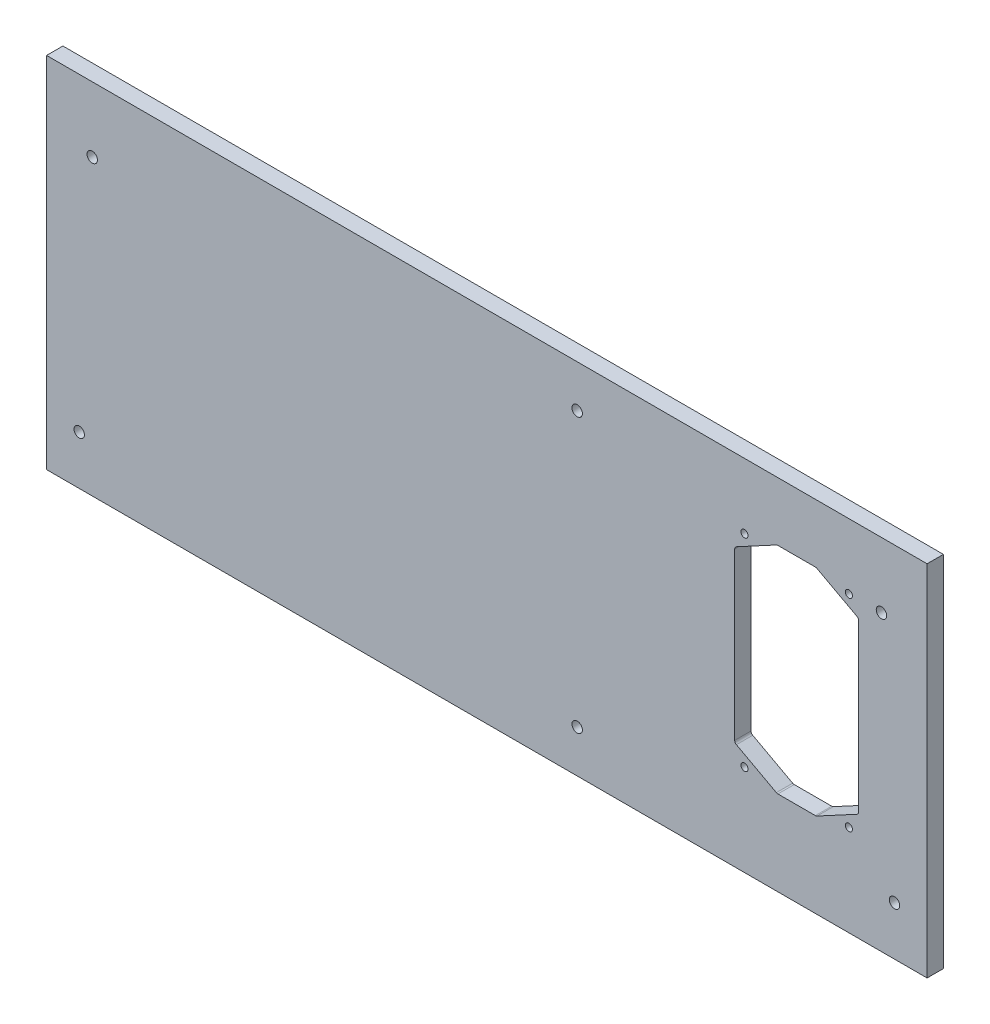
SolidWorks part; units mm, degrees
material "Polycarbonate (PC)"
ref_plane "Front Plane" through (0, 0, 0) normal (0, 0, 1) x (1, 0, 0)
ref_plane "Top Plane" through (0, 0, 0) normal (0, 1, 0) x (1, 0, 0)
ref_plane "Right Plane" through (0, 0, 0) normal (1, 0, 0) x (0, 0, -1)
sketch "Sketch1" plane through (0, 0, 0) normal (0, 0, 1) x (1, 0, 0)
  line L1 (135, -55) -> (-135, -55)
  line L2 (135, -55) -> (135, 55)
  line L3 (135, 55) -> (-135, 55)
  line L4 (-135, -55) -> (-135, 55)
  line L5 (135, -55) -> (-135, 55) construction
  line L6 (135, 55) -> (-135, -55) construction
  point P0 (0, 0)
  dimension "D1" = 110
  dimension "D2" = 270
extrude "Sheet" add sketch "Sketch1" along normal mid plane 5
sketch "Sketch4" plane through (0, 0, -2.5) normal (0, 0, -1) x (-1, 0, 0)
  line L0 (-101, 37) -> (-114, 30)
  line L1 (-89, -29) -> (-101, -29)
  line L2 (-76, -22) -> (-76, 30)
  line L3 (-89, 37) -> (-101, 37)
  line L4 (-114, -22) -> (-114, 30)
  line L5 (-76, -29) -> (-114, 37) construction
  line L6 (-76, 37) -> (-114, -29) construction
  line L7 (-79, -27) -> (-111, -27) construction
  line L8 (-79, -27) -> (-79, 35) construction
  line L9 (-79, 35) -> (-111, 35) construction
  line L10 (-111, -27) -> (-111, 35) construction
  line L11 (-79, -27) -> (-111, 35) construction
  line L12 (-79, 35) -> (-111, -27) construction
  line L13 (-101, -29) -> (-114, -22)
  line L14 (-95, 4) -> (-95, 17.8562) construction
  line L15 (-76, 30) -> (-89, 37)
  line L16 (-76, -22) -> (-89, -29)
  line L17 (-135, -55) -> (-135, 55) construction
  line L18 (135, -55) -> (-135, -55) construction
  circle A0 centre (-79, 35) radius 1.1
  circle A1 centre (-111, 35) radius 1.1
  circle A2 centre (-111, -27) radius 1.1
  circle A3 centre (-79, -27) radius 1.1
  point P0 (-95, 4)
  point P14 (-95, 4)
  dimension "D1" = 2.2
  dimension "D2" = 62
  dimension "D3" = 32
  dimension "D4" = 38
  dimension "D5" = 66
  dimension "D6" = 13
  dimension "D7" = 7
  dimension "D8" = 13
  dimension "D9" = 7
  dimension "D10" = 7
  dimension "D11" = 13
  dimension "D12" = 13
  dimension "D13" = 7
  dimension "D14" = 40
  dimension "D15" = 59
extrude "Cut-Extrude1" cut sketch "Sketch4" against normal through all
fillet "Fillet1" radius 1 8 edges at (76, 30, 0) (89, -29, 0) (101, -29, 0) (114, -22, 0) (114, 30, 0) (101, 37, 0) (89, 37, 0) (76, -22, 0)
hole_wizard "Ø3.2 (3.2) MountHoles" positions "Sketch5" profile "Sketch6" hole size "Ø3.2" standard "ANSI Metric" end condition through all
sketch "Sketch5" plane through (0, 0, -2.5) normal (0, 0, -1) x (-1, 0, 0)
  line L0 (135, -55) -> (-135, -55) construction
  line L1 (135, 55) -> (135, -55) construction
  line L2 (-135, 55) -> (135, 55) construction
  line L3 (-135, -55) -> (-135, 55) construction
  point P0 (-121, 35)
  point P2 (-125, -40)
  point P4 (125, -40)
  point P6 (121, 35)
  dimension "D1" = 15
  dimension "D2" = 10
  dimension "D3" = 20
  dimension "D4" = 14
  dimension "D5" = 14
  dimension "D6" = 10
sketch "Sketch6" plane through (121, 35, -2.5) normal (1, 0, 0) x (0, 1, 0)
  line L0 (0, 0) -> (0, 5)
  line L1 (0, 5) -> (1.6, 5)
  line L2 (1.6, 5) -> (1.6, 1.65)
  line L3 (1.6, 1.65) -> (3.25, 0)
  line L5 (3.25, 0) -> (0, 0)
  line L6 (-1.6, 1.65) -> (-3.25, 0) construction
  line L11 (0, -6.35) -> (0, 107.95) construction
  dimension "Thru Hole Dia." = 3.2
  dimension "Thru Hole Depth" = 5
  dimension "Near C'Sink Dia." = 6.5
  dimension "Near C'Sink Angle" = 90
hole_wizard "Ø3.2 (3.2) MiddlePartHoles" positions "Sketch7" profile "Sketch8" hole size "Ø3.2" standard "ANSI Metric" end condition through all
sketch "Sketch7" plane through (0, 0, -2.5) normal (0, 0, -1) x (-1, 0, 0)
  line L2 (-135, 55) -> (135, 55) construction
  line L3 (135, -55) -> (-135, -55) construction
  line L4 (135, 55) -> (135, -55) construction
  point P9 (-27.7, 42)
  point P11 (-27.7, -42)
  point P14 (0, 0)
  dimension "D1" = 13
  dimension "D2" = 13
  dimension "D3" = 162.7
sketch "Sketch8" plane through (27.7, 42, -2.5) normal (1, 0, 0) x (0, 1, 0)
  line L0 (0, 0) -> (0, 5)
  line L1 (0, 5) -> (1.6, 5)
  line L2 (1.6, 5) -> (1.6, 1.65)
  line L3 (1.6, 1.65) -> (3.25, 0)
  line L5 (3.25, 0) -> (0, 0)
  line L6 (-1.6, 1.65) -> (-3.25, 0) construction
  line L11 (0, -6.35) -> (0, 107.95) construction
  dimension "Thru Hole Dia." = 3.2
  dimension "Thru Hole Depth" = 5
  dimension "Near C'Sink Dia." = 6.5
  dimension "Near C'Sink Angle" = 90
equation "\"D5@Sketch5\"=\"D4@Sketch5\""
